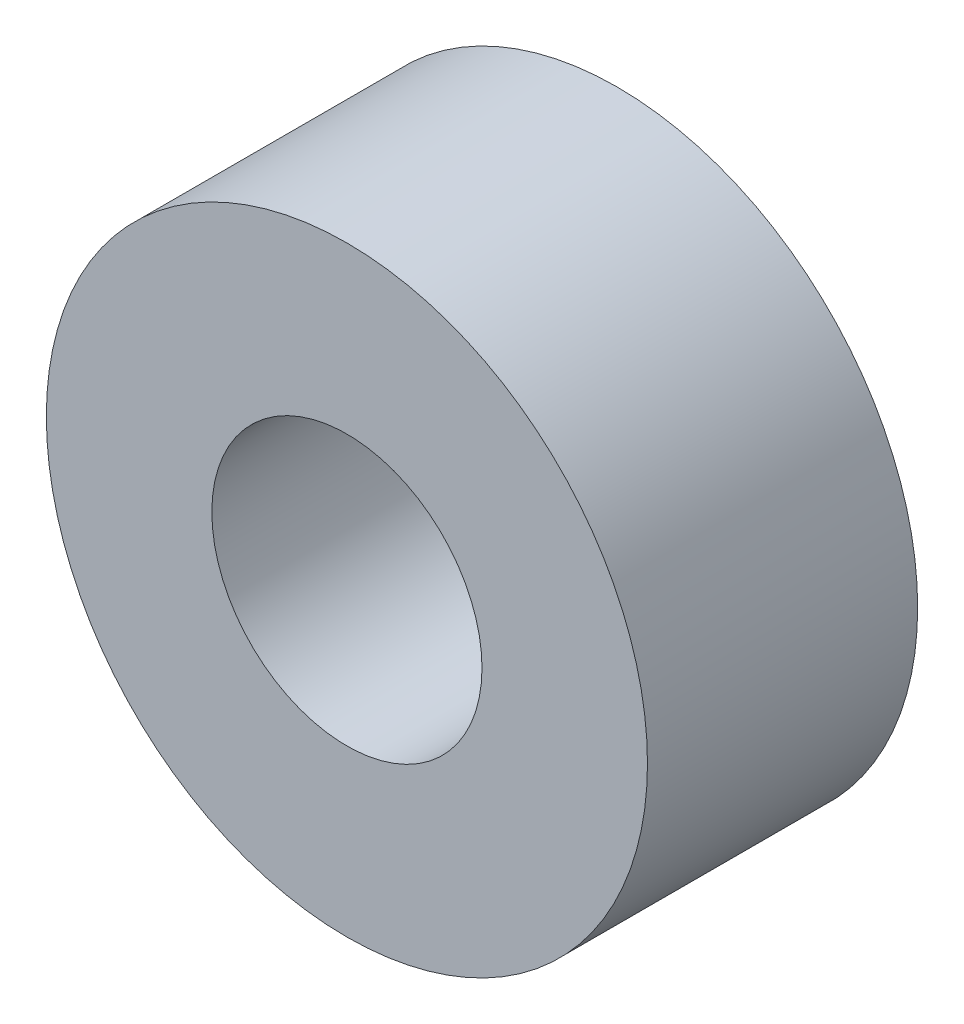
SolidWorks part; units mm, degrees
ref_plane "Front Plane" through (0, 0, 0) normal (0, 0, 1) x (1, 0, 0)
ref_plane "Top Plane" through (0, 0, 0) normal (0, 1, 0) x (1, 0, 0)
ref_plane "Right Plane" through (0, 0, 0) normal (1, 0, 0) x (0, 0, -1)
sketch "Sketch1" plane through (0, 0, 0) normal (0, 0, 1) x (1, 0, 0)
  circle A0 centre (0, 0) radius 8.9
  circle A1 centre (0, 0) radius 4
  dimension "D1" = 8
  dimension "D2" = 17.8
extrude "Boss-Extrude1" add sketch "Sketch1" along normal blind 8
